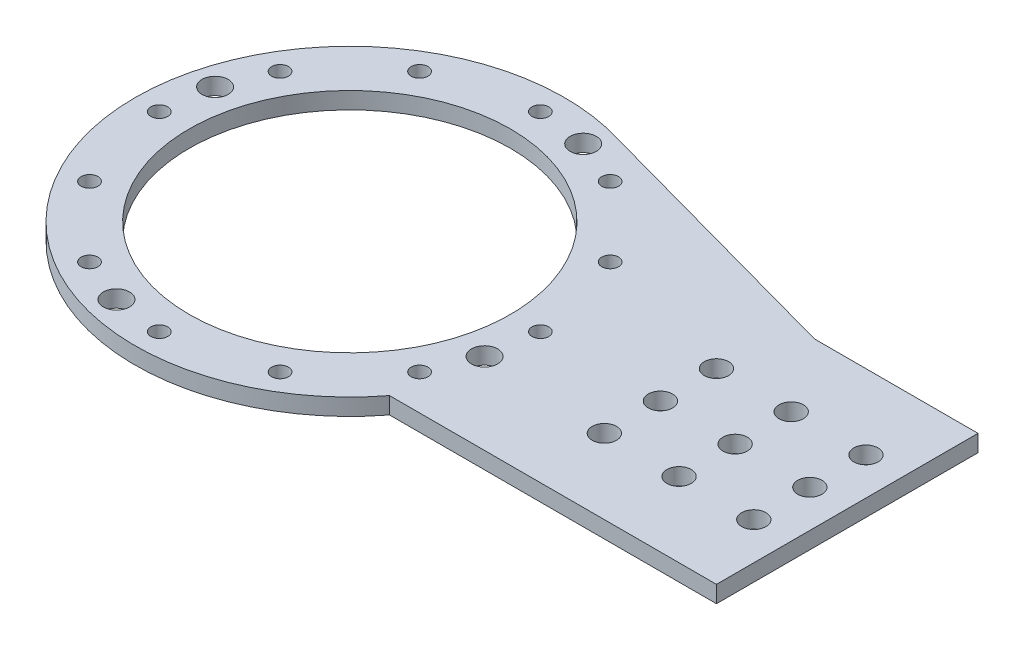
SolidWorks part; units mm, degrees
ref_plane "Front Plane" through (0, 0, 0) normal (0, 0, 1) x (1, 0, 0)
ref_plane "Top Plane" through (0, 0, 0) normal (0, 1, 0) x (1, 0, 0)
ref_plane "Right Plane" through (0, 0, 0) normal (1, 0, 0) x (0, 0, -1)
sketch "Sketch1" plane through (0, 0, 0) normal (0, 1, 0) x (1, 0, 0)
  circle A0 centre (0, 0) radius 57.5
  dimension "D1" = 115
extrude "Boss-Extrude1" add sketch "Sketch1" along normal blind 4.5
sketch "Sketch2" plane through (0, 0, 0) normal (0, 1, 0) x (1, 0, 0)
  line L0 (133.1258, 35) -> (-6.8742, 35)
  line L1 (133.1258, 35) -> (133.1258, -35)
  line L2 (-6.8742, 35) -> (-6.8742, -35)
  line L3 (133.1258, -35) -> (-6.8742, -35)
  line L4 (-6.8742, 0) -> (133.1258, 0) construction
  line L5 (63.1258, 35) -> (63.1258, -35) construction
  point P1 (63.1258, 0)
  dimension "D1" = 70
  dimension "D2" = 140
extrude "Boss-Extrude2" add sketch "Sketch2" along normal blind 4.5
sketch "Sketch3" plane through (0, 0, 0) normal (0, 1, 0) x (1, 0, 0)
  line L0 (89.3733, 35) -> (13.7685, 55.8272)
  line L1 (133.1258, 35) -> (45.6207, 35) construction
  line L2 (13.7685, 55.8272) -> (13.7685, 13.5588)
  line L3 (13.7685, 13.5588) -> (89.3733, 35)
  circle A0 centre (0, 0) radius 57.5 construction
extrude "Boss-Extrude3" add sketch "Sketch3" along normal blind 4.5
mirror "Mirror1" [suppressed] about plane through (0, 0, 0) normal (0, 0, 1)
sketch "Sketch4" plane through (0, 4.5, 0) normal (0, 1, 0) x (1, 0, 0)
  circle A0 centre (0, 0) radius 43
  dimension "D1" = 86
extrude "Cut-Extrude1" cut sketch "Sketch4" against normal through all
sketch "Sketch7" plane through (0, 4.5, 0) normal (0, 1, 0) x (1, 0, 0)
  line L0 (0, 0) -> (133.1258, 0) construction
  line L1 (133.1258, -35) -> (133.1258, 35) construction
  line L2 (123.1258, 15) -> (123.1258, -15) construction
  circle A0 centre (123.1258, 15) radius 3.25
  circle A1 centre (123.1258, -15) radius 3.25
  point P8 (123.1258, 0)
  dimension "D1" = 6.5
  dimension "D2" = 30
  dimension "D3" = 10
extrude "Cut-Extrude8" cut sketch "Sketch7" against normal through all
pattern_linear "LPattern1" count 3 spacing 20 along (-1, 0, 0) of "Cut-Extrude8"
sketch "Sketch5" plane through (0, 0, 0) normal (0, 1, 0) x (1, 0, 0)
  circle A0 centre (0, 0) radius 51 construction
  circle A1 centre (-51, 0) radius 2.25
  dimension "D1" = 4.5
  dimension "D2" = 102
extrude "Cut-Extrude5" cut sketch "Sketch5" against normal through all and the other way through all contours A1
pattern_circular "CirPattern1" count 12 over 360 about axis through (0, 0, 0) along (0, 1, 0) of "Cut-Extrude5"
sketch "Sketch11" plane through (0, 4.5, 0) normal (0, 1, 0) x (1, 0, 0)
  line L0 (52.9426, -35) -> (62.7348, -25.9656)
  line L1 (45.6207, -35) -> (133.1258, -35) construction
  line L2 (62.7348, -25.9656) -> (71.0702, -35)
  line L3 (71.0702, -35) -> (52.9426, -35)
extrude "Cut-Extrude16" [suppressed] cut sketch "Sketch11" against normal through all
sketch "Sketch12" plane through (0, 4.5, 0) normal (0, 1, 0) x (1, 0, 0)
  line L0 (0, 0) -> (-51, 0) construction
  line L1 (0, 0) -> (-49.2622, 13.1998) construction
  circle A0 centre (0, 0) radius 51 construction
  circle A1 centre (-49.2622, 13.1998) radius 3.5
  dimension "D1" = 102
  dimension "D2" = 7
  dimension "D3" = 15
extrude "Cut-Extrude17" cut sketch "Sketch12" against normal through all
pattern_circular "CirPattern2" count 4 over 360 about axis through (0, 0, 0) along (0, 1, 0) of "Cut-Extrude17"
sketch "Sketch13" plane through (0, 4.5, 0) normal (0, 1, 0) x (1, 0, 0)
  line L0 (133.1258, 0) -> (0, 0) construction
  line L1 (133.1258, -35) -> (133.1258, 35) construction
  circle A0 centre (123.1258, 0) radius 3.25
  dimension "D1" = 6.5
  dimension "D2" = 10
extrude "Cut-Extrude18" cut sketch "Sketch13" against normal blind 10 contours A0
pattern_linear "LPattern2" count 3 spacing 20 along (-1, 0, 0) of "Cut-Extrude18"
